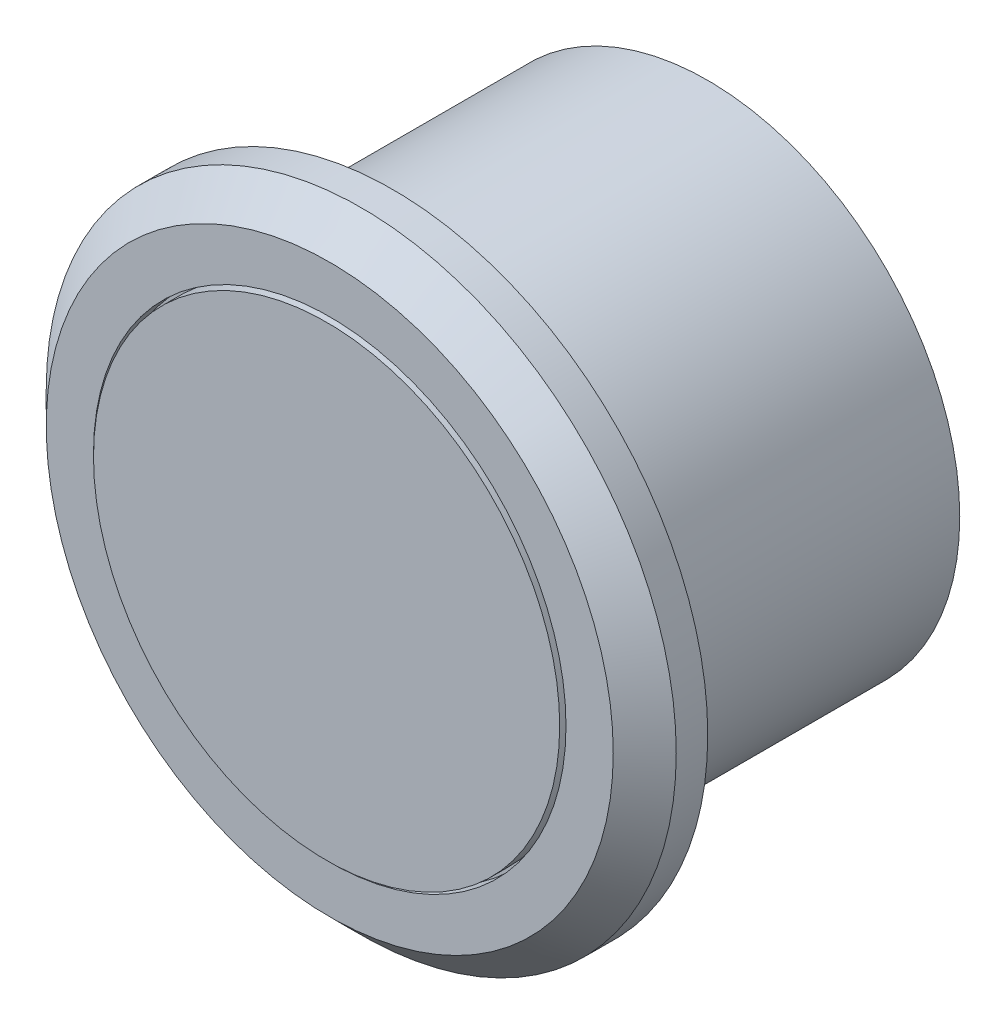
SolidWorks part; units mm, degrees
material "ABS"
ref_plane "Plan de face" through (0, 0, 0) normal (0, 0, 1) x (1, 0, 0)
ref_plane "Plan de dessus" through (0, 0, 0) normal (0, 1, 0) x (1, 0, 0)
ref_plane "Plan de droite" through (0, 0, 0) normal (1, 0, 0) x (0, 0, -1)
sketch "Esquisse1" plane through (0, 0, 0) normal (0, 0, 1) x (1, 0, 0)
  circle A0 centre (0, 0) radius 8
  dimension "D1" = 16
extrude "Boss.-Extru.1" add sketch "Esquisse1" along normal blind 10
sketch "Esquisse2" plane through (0, 0, 10) normal (0, 0, 1) x (1, 0, 0)
  circle A0 centre (0, 0) radius 10
  dimension "D1" = 20
extrude "Boss.-Extru.2" add sketch "Esquisse2" along normal blind 2
chamfer "Chanfrein1" distance 1 angle 45 1 edges at (10, 0, 12)
sketch "Esquisse3" plane through (0, 0, 12) normal (0, 0, 1) x (1, 0, 0)
  circle A0 centre (0, 0) radius 7.5
  dimension "D1" = 15
extrude "Enlèv. mat.-Extru.1" cut sketch "Esquisse3" against normal blind 0.5
sketch "Esquisse4" plane through (0, 0, 11.5) normal (0, 0, 1) x (1, 0, 0)
  circle A0 centre (0, 0) radius 7.4
  dimension "D1" = 14.8
extrude "Boss.-Extru.3" add sketch "Esquisse4" along normal blind 0.6
